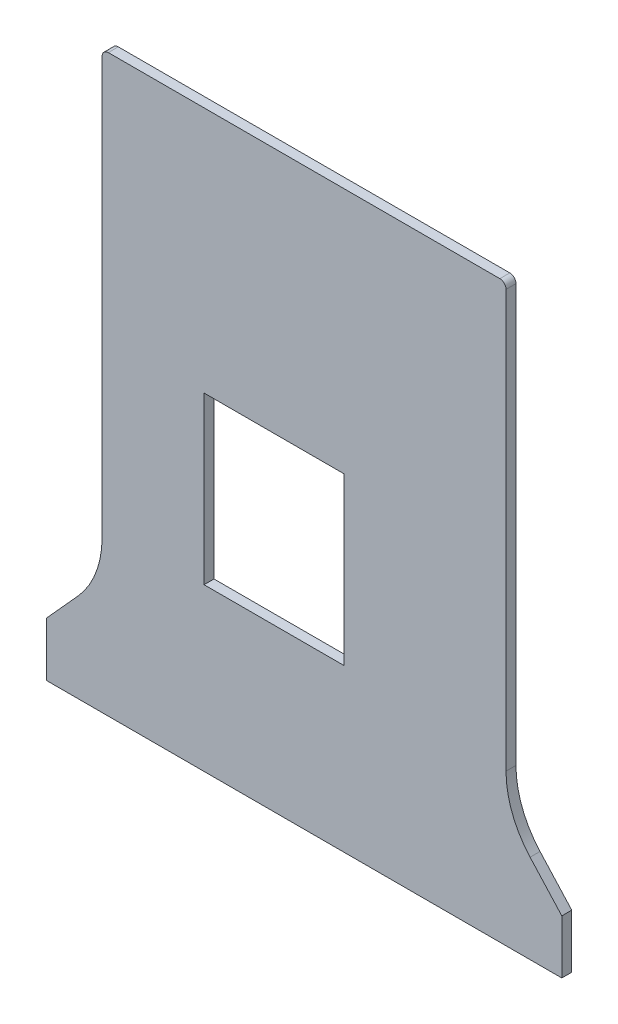
SolidWorks part; units mm, degrees
ref_plane "Front Plane" through (0, 0, 0) normal (0, 0, 1) x (1, 0, 0)
ref_plane "Top Plane" through (0, 0, 0) normal (0, 1, 0) x (1, 0, 0)
ref_plane "Right Plane" through (0, 0, 0) normal (1, 0, 0) x (0, 0, -1)
sketch "BOARD" plane through (0, 0, 0) normal (0, 0, 1) x (1, 0, 0)
  line L0 (25.68, 52.78) -> (48.18, 52.78)
  line L1 (48.18, 52.78) -> (48.18, 26.06)
  line L2 (48.18, 26.06) -> (25.68, 26.06)
  line L3 (25.68, 26.06) -> (25.68, 52.78)
  line L4 (78.1581, 14.3152) -> (83.2605, 8.69)
  line L5 (0.28, 8.69) -> (5.3737, 14.3231)
  line L6 (73.2901, 92.5299) -> (10.2701, 92.5299)
  line L7 (0.28, 0.03) -> (83.2605, 0.03)
  line L8 (83.2605, 8.69) -> (83.2605, 0.03)
  line L9 (9.27, 91.54) -> (9.27, 24.38)
  line L10 (74.2801, 91.5299) -> (74.2801, 24.3699)
  line L11 (0.28, 8.69) -> (0.28, 0.03)
  arc A0 (10.2701, 92.5299) -> (9.27, 91.54) centre (10.2737, 91.526) ccw
  arc A1 (74.2801, 91.5299) -> (73.2901, 92.5299) centre (73.2763, 91.5261) ccw
  arc A2 (74.2801, 24.3699) -> (78.1581, 14.3152) centre (89.3158, 24.3937) ccw
  arc A3 (5.3737, 14.3231) -> (9.27, 24.38) centre (-5.7656, 24.4219) ccw
ref_plane "Plane1" through (0, 0, 812.8) normal (0, 0, 1) x (1, 0, 0)
extrude "Boss-Extrude2" add sketch "BOARD" along normal blind 1.6
